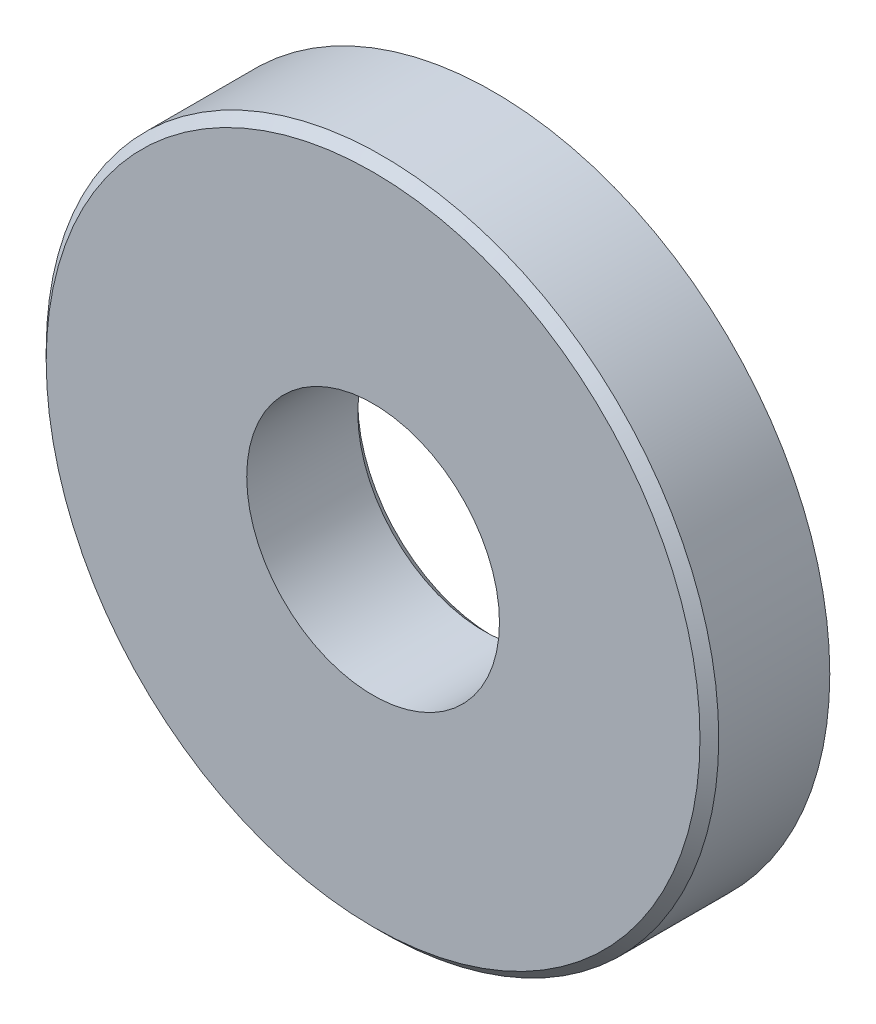
SolidWorks part; units mm, degrees
ref_plane "前视基准面" through (0, 0, 0) normal (0, 0, 1) x (1, 0, 0)
ref_plane "上视基准面" through (0, 0, 0) normal (0, 1, 0) x (1, 0, 0)
ref_plane "右视基准面" through (0, 0, 0) normal (1, 0, 0) x (0, 0, -1)
sketch "草图1" plane through (0, 0, 0) normal (0, 0, 1) x (1, 0, 0)
  circle A0 centre (0, 0) radius 4.04
  circle A1 centre (0, 0) radius 10.75
extrude "凸台-拉伸1" add sketch "草图1" along normal blind 3.85
chamfer "倒角1" distance 0.3 angle 45 1 edges at (10.75, 0, 3.85)
chamfer "倒角2" distance 0.3 angle 45 1 edges at (4.04, 0, 0)
